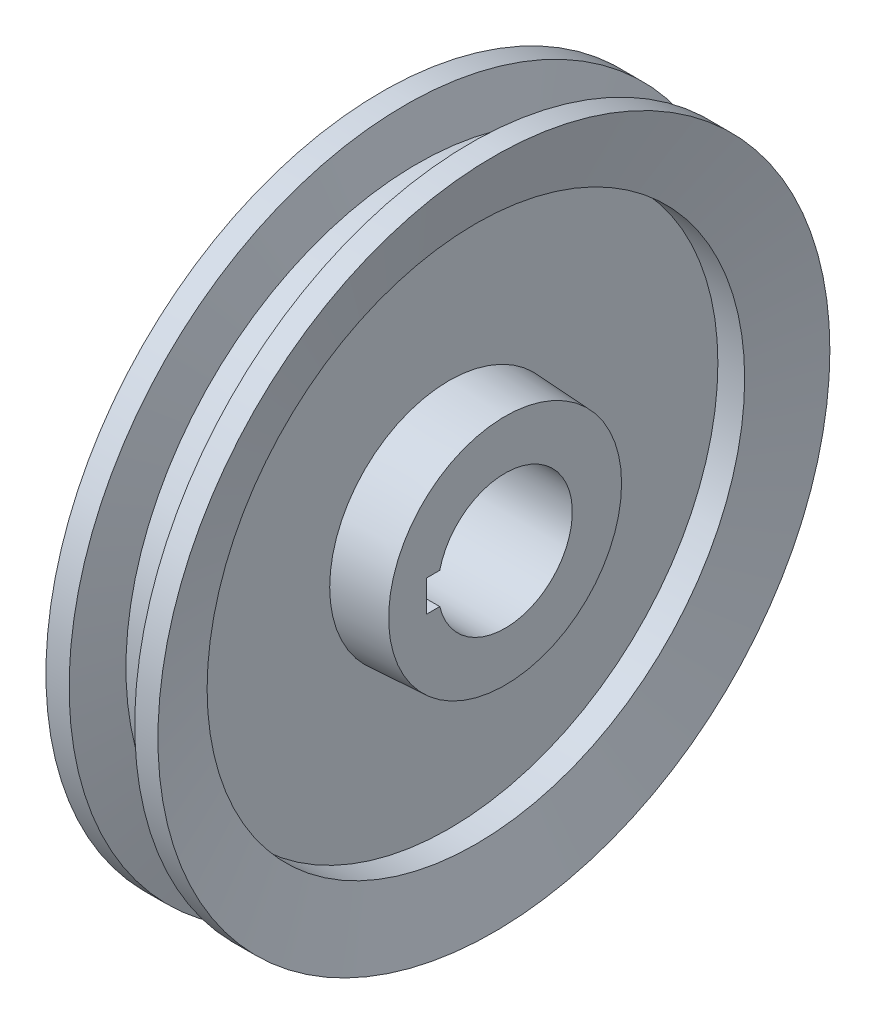
SolidWorks part; units mm, degrees
ref_plane "Front Plane" through (0, 0, 0) normal (0, 0, 1) x (1, 0, 0)
ref_plane "Top Plane" through (0, 0, 0) normal (0, 1, 0) x (1, 0, 0)
ref_plane "Right Plane" through (0, 0, 0) normal (1, 0, 0) x (0, 0, -1)
sketch "Sketch1" plane through (0, 0, 0) normal (0, 0, 1) x (1, 0, 0)
  line L0 (0, 0) -> (0, 96.7407) construction
  line L1 (0, 0) -> (-83.8128, 0) construction
  line L2 (0, 0) -> (0, 75) construction
  line L4 (12.5, 75) -> (8.4808, 60)
  line L6 (2.5, 26.6551) -> (15, 26)
  line L7 (15, 26) -> (15, 0)
  line L8 (15, 0) -> (-15, 0)
  line L9 (-15, 26) -> (-15, 0)
  line L10 (-2.5, 26.6551) -> (-15, 26)
  line L12 (-12.5, 75) -> (-8.4808, 60)
  line L13 (-8.4808, 60) -> (-2.5, 60)
  line L14 (-2.5, 60) -> (-2.5, 26.6551)
  line L15 (2.5, 60) -> (2.5, 26.6551)
  line L16 (8.4808, 60) -> (2.5, 60)
  line L17 (7.3236, 75) -> (4.6441, 65)
  line L18 (4.6441, 65) -> (-4.6441, 65)
  line L19 (7.3236, 75) -> (12.5, 75)
  line L20 (-7.3236, 75) -> (-4.6441, 65)
  line L21 (-7.3236, 75) -> (-12.5, 75)
  point P20 (0, 65)
  dimension "D1" = 30
  dimension "D2" = 15
  dimension "D3" = 26
  dimension "D4" = 3
  dimension "D5" = 5
  dimension "D6" = 25
  dimension "D7" = 30
  dimension "D8" = 60
  dimension "D9" = 5
  dimension "D10" = 10
  dimension "D11" = 15
revolve "Revolve1" add sketch "Sketch1" angle 360 about L8
sketch "Sketch2" plane through (0, 0, 0) normal (1, 0, 0) x (0, 0, -1)
  circle A0 centre (0, 0) radius 15
  dimension "D1" = 30
extrude "Cut-Extrude1" cut sketch "Sketch2" against normal through all both and the other way through all
sketch "Sketch3" plane through (0, 0, 0) normal (1, 0, 0) x (0, 0, -1)
  line L1 (0, -3.5) -> (-17.5, -3.5)
  line L2 (0, -3.5) -> (0, 3.5)
  line L3 (0, 3.5) -> (-17.5, 3.5)
  line L4 (-17.5, -3.5) -> (-17.5, 3.5)
  circle A0 centre (0, 0) radius 15 construction
  point P4 (-6.4211, -3.5279)
  dimension "D1" = 7
  dimension "D2" = 32.5
extrude "Cut-Extrude2" cut sketch "Sketch3" against normal through all both and the other way through all
